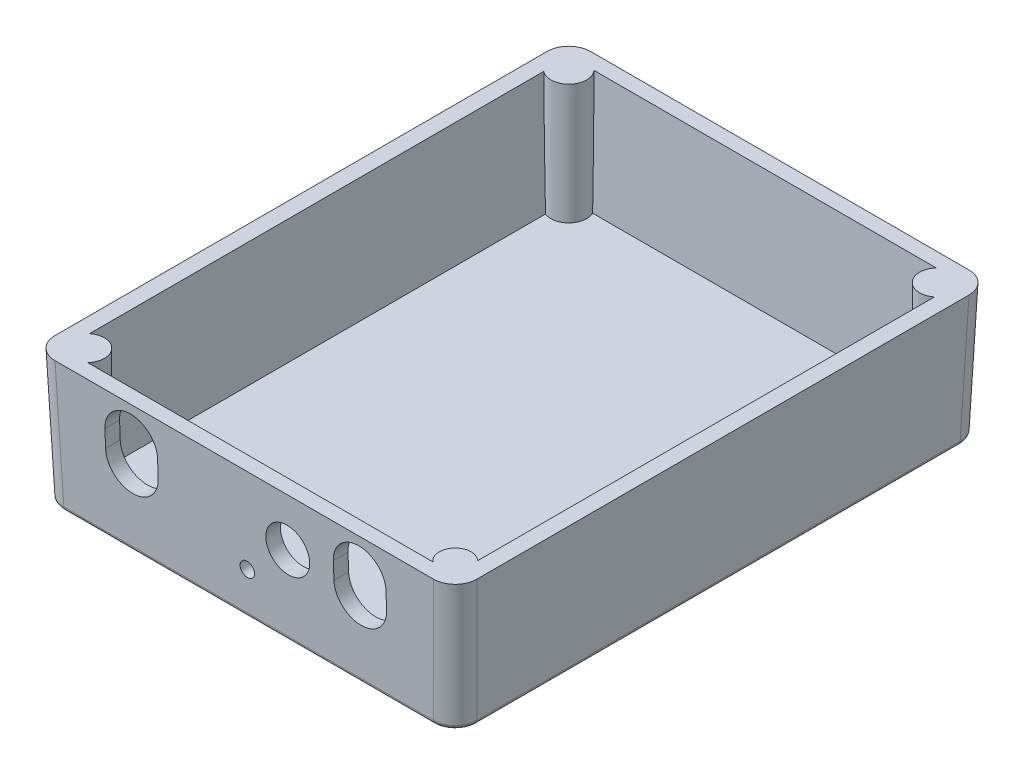
SolidWorks part; units mm, degrees
ref_plane "Front Plane" through (0, 0, 0) normal (0, 0, 1) x (1, 0, 0)
ref_plane "Top Plane" through (0, 0, 0) normal (0, 1, 0) x (1, 0, 0)
ref_plane "Right Plane" through (0, 0, 0) normal (1, 0, 0) x (0, 0, -1)
sketch "Sketch1" plane through (0, 0, 0) normal (0, 1, 0) x (1, 0, 0)
  line L1 (0, 0) -> (94.1, 0)
  line L2 (0, 0) -> (0, 120)
  line L3 (0, 120) -> (94.1, 120)
  line L4 (94.1, 0) -> (94.1, 120)
  dimension "D1" = 94.1
  dimension "D2" = 120
extrude "Boss-Extrude1" add sketch "Sketch1" along normal blind 29.82 draft 2 draft outward yes
fillet "Fillet1" radius 4.95 4 edges at (94.6207, 14.91, 0.5207) (-0.5207, 14.91, 0.5207) (94.6207, 14.91, -120.5207) (-0.5207, 14.91, -120.5207)
ref_plane "Plane1" through (0, 29.82, 0) normal (0, 1, 0) x (1, 0, 0)
sketch "Sketch3" plane through (0, 29.82, 0) normal (0, 1, 0) x (1, 0, 0)
  line L4 (2.52, 2.3) -> (91.58, 2.3)
  line L5 (2.52, 2.3) -> (2.52, 117.7)
  line L6 (2.52, 117.7) -> (91.58, 117.7)
  line L7 (91.58, 2.3) -> (91.58, 117.7)
  line L8 (2.52, 2.3) -> (91.58, 117.7) construction
  line L9 (2.52, 117.7) -> (91.58, 2.3) construction
  point P6 (46.58, 60.47)
  dimension "D1" = 89.06
  dimension "D2" = 115.4
extrude "Cut-Extrude1" cut sketch "Sketch3" against normal blind 27.4 draft 2
sketch "Sketch4" plane through (0, 0, 0) normal (0, 1, 0) x (1, 0, 0)
  circle A0 centre (5.0282, 114.9718) radius 4.065
  circle A1 centre (89.0718, 114.9718) radius 4.065
  circle A2 centre (5.0282, 5.0282) radius 4.065
  circle A3 centre (89.0718, 5.0282) radius 3.6125
extrude "Boss-Extrude2" add sketch "Sketch4" along normal blind 29.82
sketch "Sketch6" plane through (0, 0, 0) normal (0, 0, 1) x (1, 0, 0)
  line L0 (15.015, 21.82) -> (15.015, 17.82)
  line L1 (27.015, 21.82) -> (27.015, 17.82)
  line L3 (67.085, 21.82) -> (67.085, 17.82)
  line L4 (79.085, 21.82) -> (79.085, 17.82)
  circle A0 centre (47.05, 9.82) radius 1.65
  circle A1 centre (21.015, 17.82) radius 6
  circle A2 centre (73.085, 17.82) radius 6
  circle A3 centre (56.575, 18.57) radius 5
  circle A4 centre (21.015, 21.82) radius 6
  circle A5 centre (73.085, 21.82) radius 6
extrude "Cut-Extrude2" cut sketch "Sketch6" against normal blind 8 and the other way through all from offset 3
ref_plane "Plane2" through (0, 0, 0) normal (0, -1, 0) x (-1, 0, 0)
sketch "Sketch8" plane through (0, 0, 0) normal (0, -1, 0) x (-1, 0, 0)
  line L0 (-47.05, 121.0413) -> (-47.05, -1.0413) construction
  line L1 (-90.1944, 121.0413) -> (-3.9056, 121.0413) construction
  line L2 (-3.9056, -1.0413) -> (-90.1944, -1.0413) construction
  line L3 (1.0413, 60) -> (-95.1413, 60) construction
  line L6 (1.0413, 116.0944) -> (1.0413, 3.9056) construction
  line L7 (-95.1413, 3.9056) -> (-95.1413, 116.0944) construction
  circle A0 centre (-71.815, 90.353) radius 2.625
  circle A1 centre (-71.815, 103.053) radius 6.5
extrude "Cut-Extrude3" cut sketch "Sketch8" against normal blind 5
fillet "Fillet2" radius 1 8 edges at (1.4486, 0, -1.4486) (0, 0, -60) (1.4486, 0, -118.5514) (47.05, 0, -120) (92.6514, 0, -118.5514) (94.1, 0, -60) (92.6514, 0, -1.4486) (47.05, 0, 0)
sketch "Sketch9" plane through (0, 0, 0) normal (0, 0, 1) x (1, 0, 0)
  line L0 (21.015, 11.82) -> (21.015, 15.82)
  arc A0 (15.015, 17.82) -> (27.015, 17.82) centre (21.015, 17.82) ccw construction
sketch "Sketch10" plane through (0, 0, 0) normal (0, 0, 1) x (1, 0, 0)
  line L1 (0, 0) -> (94.1, 0)
  line L2 (0, 0) -> (0, 120)
  line L3 (0, 120) -> (94.1, 120)
  line L4 (94.1, 0) -> (94.1, 120)
  dimension "D1" = 94.1
  dimension "D2" = 120
ref_plane "Plane3" through (0, 29.82, 0) normal (0, 1, 0) x (1, 0, 0)
